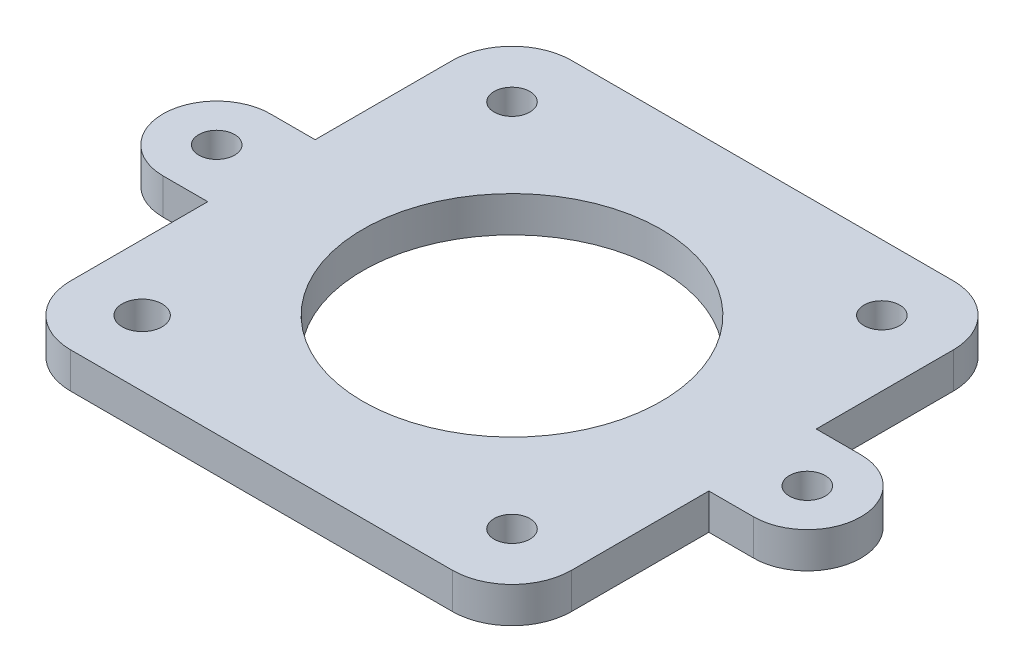
SolidWorks part; units mm, degrees
ref_plane "Front Plane" through (0, 0, 0) normal (0, 0, 1) x (1, 0, 0)
ref_plane "Top Plane" through (0, 0, 0) normal (0, 1, 0) x (1, 0, 0)
ref_plane "Right Plane" through (0, 0, 0) normal (1, 0, 0) x (0, 0, -1)
sketch "Sketch1" plane through (0, 0, 0) normal (0, 1, 0) x (1, 0, 0)
  line L1 (-16, -21) -> (16, -21)
  line L2 (-21, -16) -> (-21, 16)
  line L3 (-16, 21) -> (16, 21)
  line L4 (21, -16) -> (21, 16)
  line L5 (-21, -21) -> (21, 21) construction
  line L6 (-21, 21) -> (21, -21) construction
  circle A0 centre (15.5, 15.5) radius 1.5
  circle A1 centre (15.5, -15.5) radius 1.5
  circle A2 centre (-15.5, 15.5) radius 1.5
  circle A3 centre (-15.5, -15.5) radius 1.6729
  arc A4 (-16, -21) -> (-21, -16) centre (-16, -16) cw
  arc A5 (16, -21) -> (21, -16) centre (16, -16) ccw
  arc A6 (16, 21) -> (21, 16) centre (16, 16) cw
  arc A7 (-21, 16) -> (-16, 21) centre (-16, 16) cw
  point P0 (0, 0)
  dimension "D3" = 3
  dimension "D4" = 3
  dimension "D5" = 5.5
  dimension "D6" = 5.5
  dimension "D7" = 5.5
  dimension "D8" = 5.5
  dimension "D9" = 3
  dimension "D12" = 3.3459
  dimension "D13" = 5.5
  dimension "D15" = 5
  dimension "D1" = 42
  dimension "D2" = 42
  dimension "D10" = 5.5
  dimension "D11" = 5.5
  dimension "D14" = 5.5
extrude "Boss-Extrude1" add sketch "Sketch1" along normal blind 3
sketch "Sketch2" plane through (0, 3, 0) normal (0, 1, 0) x (1, 0, 0)
  circle A0 centre (0, 0) radius 12.5
  dimension "D1" = 25
extrude "Cut-Extrude1" cut sketch "Sketch2" against normal through all
sketch "Sketch3" plane through (0, 3, 0) normal (0, 1, 0) x (1, 0, 0)
  line L0 (-24.75, 0) -> (-23.25, 0) construction
  line L1 (-24.75, 4.5) -> (-21, 4.5)
  line L2 (-21, 16) -> (-21, -16) construction
  line L3 (-24.75, -4.5) -> (-21, -4.5)
  line L4 (24.75, -4.5) -> (21, -4.5)
  line L7 (24.75, 4.5) -> (21, 4.5)
  line L10 (23.25, 0) -> (24.75, 0) construction
  line L11 (-21, 4.5) -> (-21, -4.5)
  line L12 (21, -4.5) -> (21, 4.5)
  circle A0 centre (-24.75, 0) radius 1.5
  circle A1 centre (24.75, 0) radius 1.5
  arc A2 (-24.75, 4.5) -> (-24.75, -4.5) centre (-24.75, 0) ccw
  arc A3 (24.75, -4.5) -> (24.75, 4.5) centre (24.75, 0) ccw
  circle A4 centre (-24.75, 0) radius 4.5 construction
  circle A5 centre (24.75, 0) radius 4.5 construction
  dimension "D1" = 3
  dimension "D2" = 3
  dimension "D6" = 4.5
  dimension "D8" = 3.75
  dimension "D9" = 4.5
  dimension "D12" = 3
  dimension "D3" = 49.5
  dimension "D5" = 3.75
  dimension "D7" = 9
  dimension "D10" = 3.75
  dimension "D11" = 9
  dimension "D13" = 3.75
  dimension "D4" = 3
extrude "Boss-Extrude2" add sketch "Sketch3" against normal up to vertex (3 mm away)
